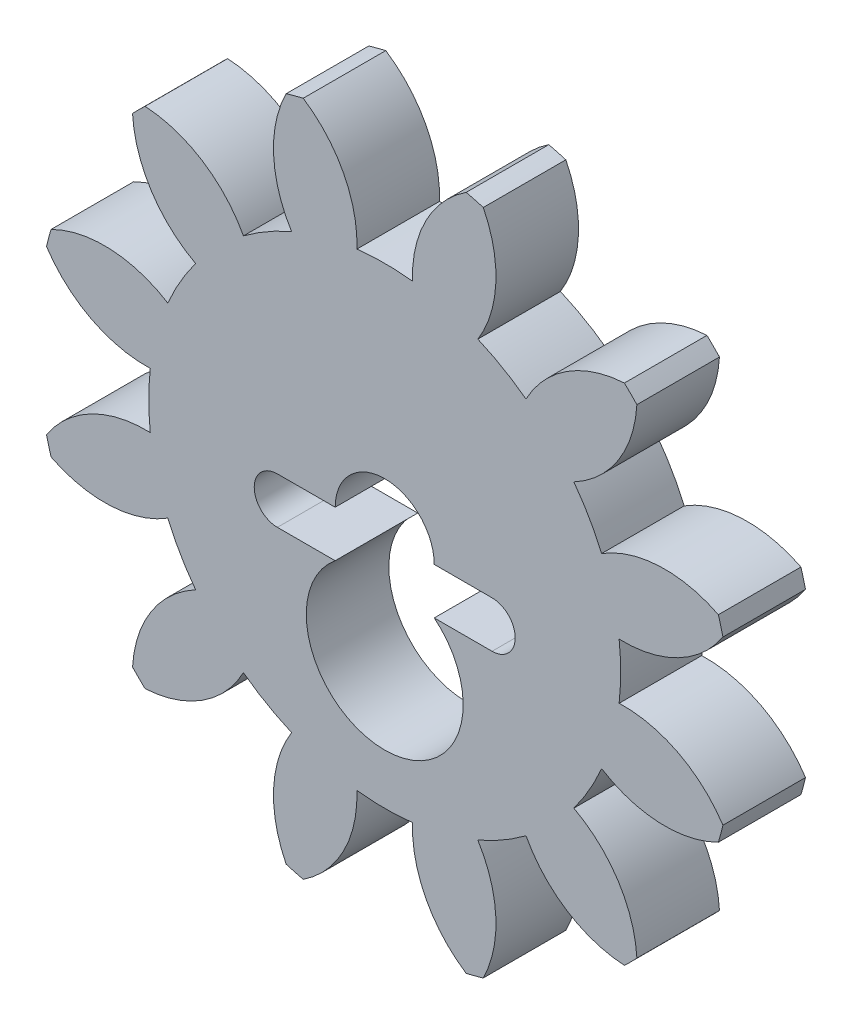
SolidWorks part; units mm, degrees
material "Ti-6Al-4VSolution treated and aged (SS)"
ref_plane "Front Plane" through (0, 0, 0) normal (0, 0, 1) x (1, 0, 0)
ref_plane "Top Plane" through (0, 0, 0) normal (0, 1, 0) x (1, 0, 0)
ref_plane "Right Plane" through (0, 0, 0) normal (1, 0, 0) x (0, 0, -1)
sketch "Sketch1" plane through (0, 0, 0) normal (0, 0, 1) x (1, 0, 0)
  line L4 (-3.302, -1.4244) -> (-1.524, -1.4244)
  line L5 (1.524, -1.4244) -> (3.302, -1.4244)
  line L6 (-1.524, 0) -> (-3.302, 0)
  line L7 (1.524, 0) -> (3.302, 0)
  arc A0 (-7.7573, 7.373) -> (-5.8176, 4.3463) centre (-4.0941, 7.5857) ccw
  arc A1 (-5.8176, 4.3463) -> (-6.6728, 2.865) centre (0, 0) ccw
  arc A2 (-6.6728, 2.865) -> (-10.2638, 3.0315) centre (-8.6165, -0.2472) ccw
  arc A3 (-10.2638, 3.0315) -> (-10.4045, 2.5065) centre (0, 0) ccw
  arc A4 (-10.4045, 2.5065) -> (-7.2113, 0.8553) centre (-7.3385, 4.5224) ccw
  arc A5 (-7.2113, 0.8553) -> (-7.2113, -0.8553) centre (0, 0) ccw
  arc A6 (-7.2113, -0.8553) -> (-10.4045, -2.5065) centre (-7.3385, -4.5224) ccw
  arc A7 (-10.4045, -2.5065) -> (-10.2638, -3.0315) centre (0, 0) ccw
  arc A8 (-10.2638, -3.0315) -> (-6.6728, -2.865) centre (-8.6165, 0.2472) ccw
  arc A9 (-6.6728, -2.865) -> (-5.8176, -4.3463) centre (0, 0) ccw
  arc A10 (-5.8176, -4.3463) -> (-7.7573, -7.373) centre (-4.0941, -7.5857) ccw
  arc A11 (-7.7573, -7.373) -> (-7.373, -7.7573) centre (0, 0) ccw
  arc A12 (-7.373, -7.7573) -> (-4.3463, -5.8176) centre (-7.5857, -4.0941) ccw
  arc A13 (-4.3463, -5.8176) -> (-2.865, -6.6728) centre (0, 0) ccw
  arc A14 (-2.865, -6.6728) -> (-3.0315, -10.2638) centre (0.2472, -8.6165) ccw
  arc A15 (-3.0315, -10.2638) -> (-2.5065, -10.4045) centre (0, 0) ccw
  arc A16 (-2.5065, -10.4045) -> (-0.8553, -7.2113) centre (-4.5224, -7.3385) ccw
  arc A17 (-0.8553, -7.2113) -> (0.8553, -7.2113) centre (0, 0) ccw
  arc A18 (0.8553, -7.2113) -> (2.5065, -10.4045) centre (4.5224, -7.3385) ccw
  arc A19 (2.5065, -10.4045) -> (3.0315, -10.2638) centre (0, 0) ccw
  arc A20 (3.0315, -10.2638) -> (2.865, -6.6728) centre (-0.2472, -8.6165) ccw
  arc A21 (2.865, -6.6728) -> (4.3463, -5.8176) centre (0, 0) ccw
  arc A22 (4.3463, -5.8176) -> (7.373, -7.7573) centre (7.5857, -4.0941) ccw
  arc A23 (7.373, -7.7573) -> (7.7573, -7.373) centre (0, 0) ccw
  arc A24 (7.7573, -7.373) -> (5.8176, -4.3463) centre (4.0941, -7.5857) ccw
  arc A25 (5.8176, -4.3463) -> (6.6728, -2.865) centre (0, 0) ccw
  arc A26 (6.6728, -2.865) -> (10.2638, -3.0315) centre (8.6165, 0.2472) ccw
  arc A27 (10.2638, -3.0315) -> (10.4045, -2.5065) centre (0, 0) ccw
  arc A28 (10.4045, -2.5065) -> (7.2113, -0.8553) centre (7.3385, -4.5224) ccw
  arc A29 (7.2113, -0.8553) -> (7.2113, 0.8553) centre (0, 0) ccw
  arc A30 (7.2113, 0.8553) -> (10.4045, 2.5065) centre (7.3385, 4.5224) ccw
  arc A31 (10.4045, 2.5065) -> (10.2638, 3.0315) centre (0, 0) ccw
  arc A32 (10.2638, 3.0315) -> (6.6728, 2.865) centre (8.6165, -0.2472) ccw
  arc A33 (6.6728, 2.865) -> (5.8176, 4.3463) centre (0, 0) ccw
  arc A34 (5.8176, 4.3463) -> (7.7573, 7.373) centre (4.0941, 7.5857) ccw
  arc A35 (7.7573, 7.373) -> (7.373, 7.7573) centre (0, 0) ccw
  arc A36 (7.373, 7.7573) -> (4.3463, 5.8176) centre (7.5857, 4.0941) ccw
  arc A37 (4.3463, 5.8176) -> (2.865, 6.6728) centre (0, 0) ccw
  arc A38 (2.865, 6.6728) -> (3.0315, 10.2638) centre (-0.2472, 8.6165) ccw
  arc A39 (3.0315, 10.2638) -> (2.5065, 10.4045) centre (0, 0) ccw
  arc A40 (2.5065, 10.4045) -> (0.8553, 7.2113) centre (4.5224, 7.3385) ccw
  arc A41 (0.8553, 7.2113) -> (-0.8553, 7.2113) centre (0, 0) ccw
  arc A42 (-0.8553, 7.2113) -> (-2.5065, 10.4045) centre (-4.5224, 7.3385) ccw
  arc A43 (-2.5065, 10.4045) -> (-3.0315, 10.2638) centre (0, 0) ccw
  arc A44 (-3.0315, 10.2638) -> (-2.865, 6.6728) centre (0.2472, 8.6165) ccw
  arc A45 (-2.865, 6.6728) -> (-4.3463, 5.8176) centre (0, 0) ccw
  arc A46 (-4.3463, 5.8176) -> (-7.373, 7.7573) centre (-7.5857, 4.0941) ccw
  arc A47 (-7.373, 7.7573) -> (-7.7573, 7.373) centre (0, 0) ccw
  arc A48 (1.524, 0) -> (-1.524, 0) centre (0, 0) ccw
  arc A49 (-3.302, 0) -> (-3.302, -1.4244) centre (-3.302, -0.7122) ccw
  arc A50 (-1.524, -1.4244) -> (1.524, -1.4244) centre (0, -3.2952) ccw
  arc A51 (3.302, -1.4244) -> (3.302, 0) centre (3.302, -0.7122) ccw
  dimension "D1" = 3.048
  dimension "D2" = 1.778
  dimension "D3" = 4.826
  dimension "D4" = 1.778
extrude "Boss-Extrude1" add sketch "Sketch1" along normal blind 2.54 contours A48 A50
